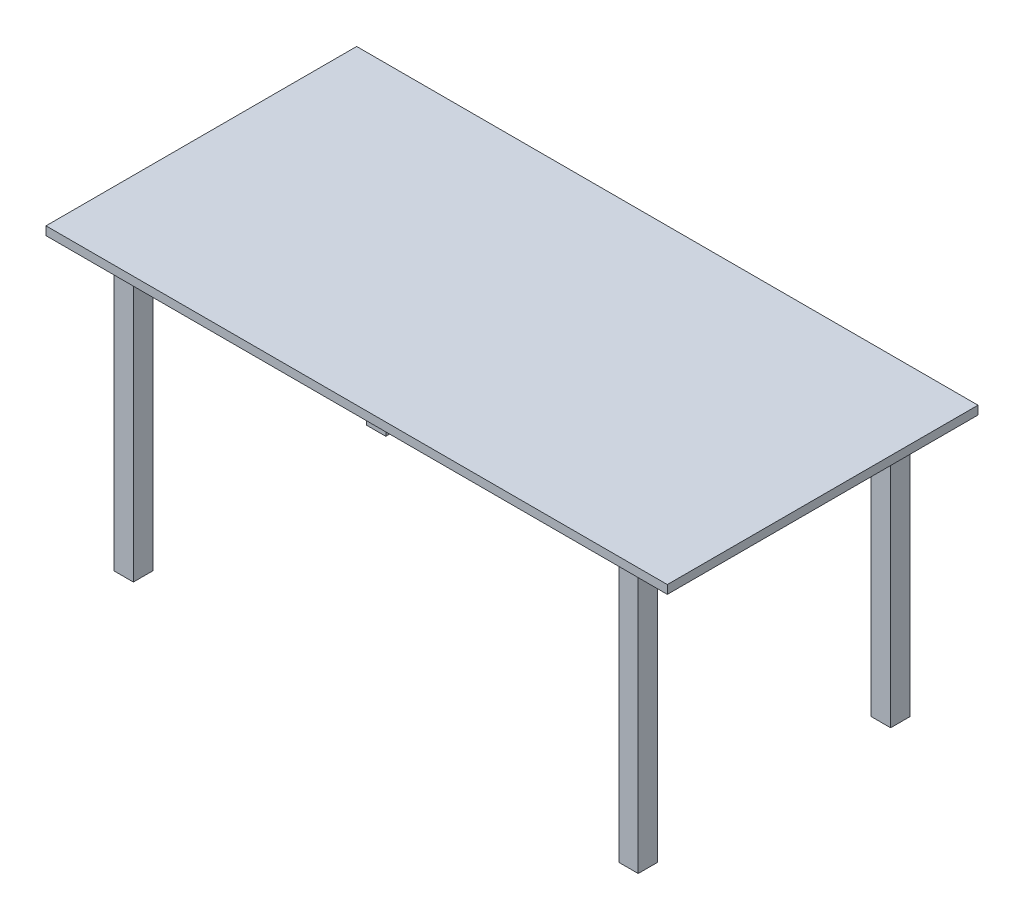
SolidWorks part; units mm, degrees
ref_plane "Front Plane" through (0, 0, 0) normal (0, 0, 1) x (1, 0, 0)
ref_plane "Top Plane" through (0, 0, 0) normal (0, 1, 0) x (1, 0, 0)
ref_plane "Right Plane" through (0, 0, 0) normal (1, 0, 0) x (0, 0, -1)
sketch "Sketch1" plane through (0, 0, 0) normal (0, 1, 0) x (1, 0, 0)
  line L1 (-800, 400) -> (800, 400)
  line L2 (-800, 400) -> (-800, -400)
  line L3 (-800, -400) -> (800, -400)
  line L4 (800, 400) -> (800, -400)
  line L5 (-800, 400) -> (800, -400) construction
  line L6 (-800, -400) -> (800, 400) construction
  point P0 (0, 0)
  dimension "D1" = 1600
  dimension "D2" = 800
extrude "Boss-Extrude1" add sketch "Sketch1" along normal blind 22
sketch "Sketch2" plane through (0, 0, 0) normal (0, -1, 0) x (1, 0, 0)
  line L0 (-800, 400) -> (800, -400) construction
  line L1 (0, 400) -> (0, -400) construction
  line L2 (-800, 400) -> (800, 400) construction
  line L3 (800, -400) -> (-800, -400) construction
  line L4 (-800, 0) -> (800, 0) construction
  line L5 (-800, -400) -> (-800, 400) construction
  line L6 (800, 400) -> (800, -400) construction
  line L7 (675, 300) -> (625, 300)
  line L8 (-675, 350) -> (-625, 350)
  line L9 (-675, 350) -> (-675, 300)
  line L10 (-675, 300) -> (-625, 300)
  line L11 (-625, 350) -> (-625, 300)
  line L12 (-675, 350) -> (-625, 300) construction
  line L13 (-675, 300) -> (-625, 350) construction
  line L14 (625, 350) -> (625, 300)
  line L15 (675, 350) -> (625, 350)
  line L16 (675, 350) -> (675, 300)
  line L17 (-675, -350) -> (-675, -300)
  line L18 (-675, -350) -> (-625, -350)
  line L19 (-625, -350) -> (-625, -300)
  line L20 (-675, -300) -> (-625, -300)
  line L21 (675, -350) -> (675, -300)
  line L22 (675, -350) -> (625, -350)
  line L23 (625, -350) -> (625, -300)
  line L24 (675, -300) -> (625, -300)
  point P16 (-650, 325)
  dimension "D1" = 50
  dimension "D2" = 150
extrude "Boss-Extrude2" add sketch "Sketch2" along normal blind 710
